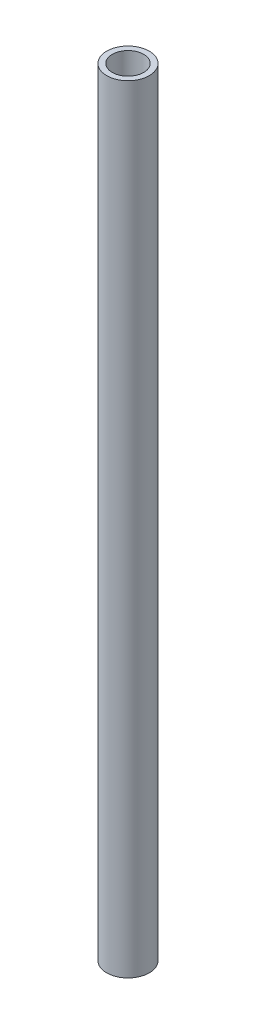
SolidWorks part; units mm, degrees
ref_plane "Alzado" through (0, 0, 0) normal (0, 0, 1) x (1, 0, 0)
ref_plane "Planta" through (0, 0, 0) normal (0, 1, 0) x (1, 0, 0)
ref_plane "Vista lateral" through (0, 0, 0) normal (1, 0, 0) x (0, 0, -1)
sketch "Croquis1" plane through (0, 0, 0) normal (0, 1, 0) x (1, 0, 0)
  circle A0 centre (0, 0) radius 8.5
  circle A1 centre (0, 0) radius 11.5
  dimension "D1" = 17
  dimension "D2" = 3
extrude "Saliente-Extruir1" add sketch "Croquis1" along normal mid plane 420
